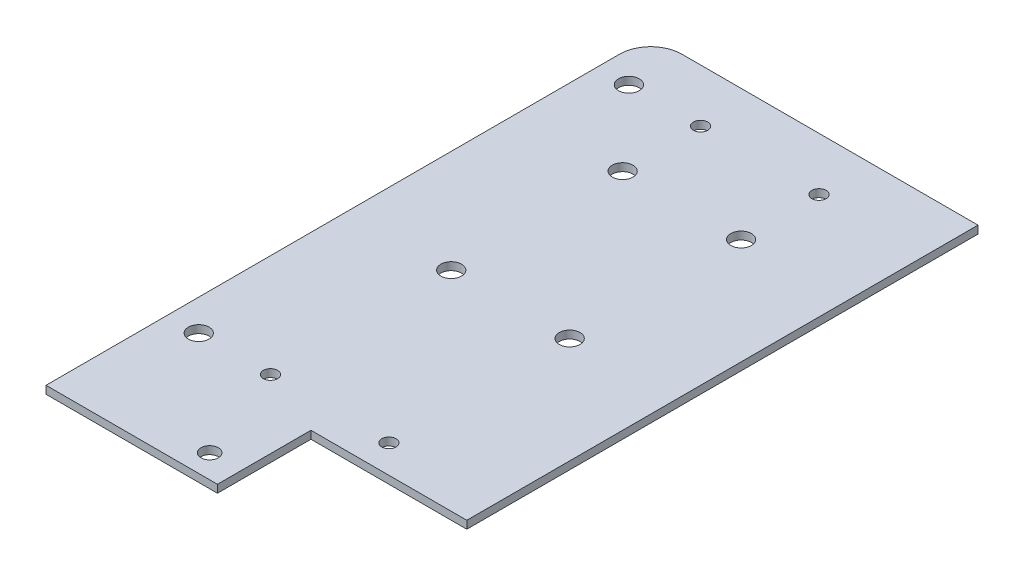
SolidWorks part; units mm, degrees
ref_plane "Front Plane" through (0, 0, 0) normal (0, 0, 1) x (1, 0, 0)
ref_plane "Top Plane" through (0, 0, 0) normal (0, 1, 0) x (1, 0, 0)
ref_plane "Right Plane" through (0, 0, 0) normal (1, 0, 0) x (0, 0, -1)
sketch "Sketch1" plane through (0, 0, 0) normal (0, 1, 0) x (1, 0, 0)
  line L0 (-14.7135, 74.2099) -> (-14.7135, -22.7901)
  line L1 (-14.7135, -22.7901) -> (12.7865, -22.7901)
  line L2 (12.7865, -22.7901) -> (12.7865, -7.7901)
  line L3 (12.7865, -7.7901) -> (37.7865, -7.7901)
  line L4 (37.7865, -7.7901) -> (37.7865, 74.2099)
  line L5 (37.7865, 74.2099) -> (-14.7135, 74.2099)
  circle A0 centre (-9.7135, 65.7099) radius 1.66
  circle A1 centre (1.7865, 65.7099) radius 1.15
  circle A2 centre (20.7865, 65.7099) radius 1.15
  circle A3 centre (1.7865, 53.2099) radius 1.66
  circle A4 centre (1.7865, 25.7099) radius 1.66
  circle A5 centre (20.7865, 53.2099) radius 1.66
  circle A6 centre (20.7865, 25.7099) radius 1.66
  circle A7 centre (1.7865, -3.2901) radius 1.15
  circle A8 centre (20.7865, -3.2901) radius 1.15
  circle A9 centre (-9.7135, -3.2901) radius 1.66
  circle A10 centre (7.7865, -19.0401) radius 1.4
  dimension "D5" = 3.32
  dimension "D6" = 2.3
  dimension "D7" = 2.8
  dimension "D8" = 3.32
  dimension "D1" = 52.5
  dimension "D2" = 97
  dimension "D3" = 15
  dimension "D4" = 25
  dimension "D9" = 5
  dimension "D10" = 16.5
  dimension "D11" = 19
  dimension "D12" = 21
  dimension "D13" = 8.5
  dimension "D14" = 48.5
  dimension "D15" = 4.5
  dimension "D16" = 5
  dimension "D17" = 3.75
extrude "Boss-Extrude1" add sketch "Sketch1" along normal blind 1.25
fillet "Fillet1" radius 5 1 edges at (-14.7135, 0.625, -74.2099)
